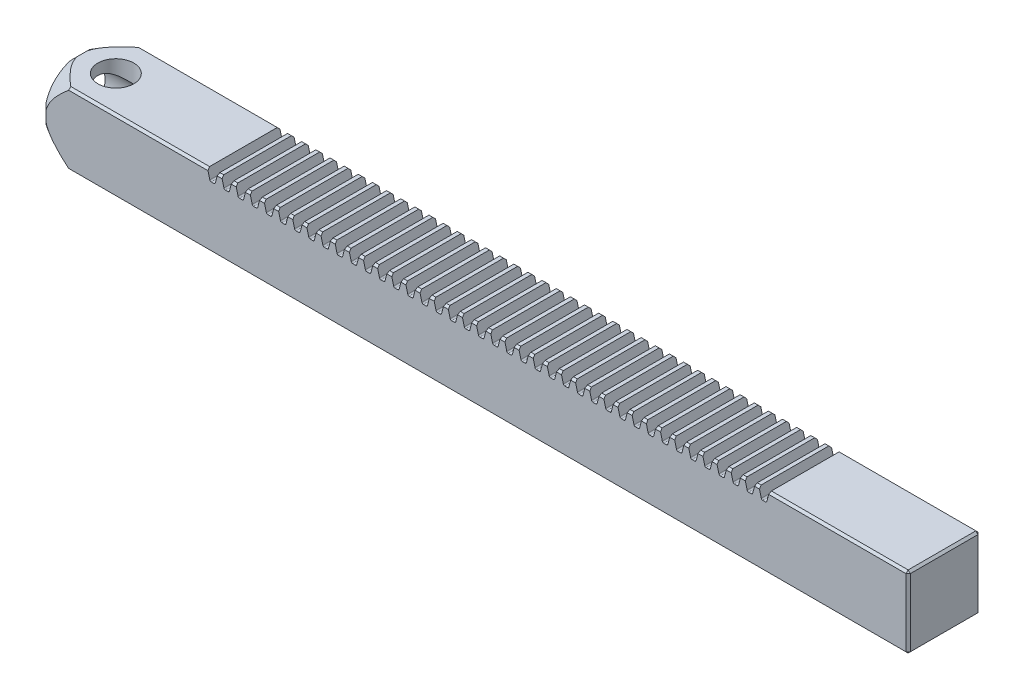
SolidWorks part; units mm, degrees
ref_plane "Front Plane" through (0, 0, 0) normal (0, 0, 1) x (1, 0, 0)
ref_plane "Top Plane" through (0, 0, 0) normal (0, 1, 0) x (1, 0, 0)
ref_plane "Right Plane" through (0, 0, 0) normal (1, 0, 0) x (0, 0, -1)
sketch "Sketch1" plane through (0, 0, 0) normal (1, 0, 0) x (0, 0, -1)
  line L1 (0.5, 0.5) -> (-0.5, 0.5)
  line L2 (0.5, 0.5) -> (0.5, -0.5)
  line L3 (0.5, -0.5) -> (-0.5, -0.5)
  line L4 (-0.5, 0.5) -> (-0.5, -0.5)
  line L5 (0.5, 0.5) -> (-0.5, -0.5) construction
  line L6 (0.5, -0.5) -> (-0.5, 0.5) construction
  point P0 (0, 0)
  dimension "D1" = 1
  dimension "D2" = 1
extrude "Boss-Extrude1" add sketch "Sketch1" along normal blind 12
chamfer "Chamfer1" distance 0.03 angle 45 12 edges at (12, 0, -0.5) (0, 0, -0.5) (12, -0.5, 0) (6, -0.5, -0.5) (0, -0.5, 0) (12, 0, 0.5) (6, -0.5, 0.5) (0, 0, 0.5) (6, 0.5, -0.5) (12, 0.5, 0) (6, 0.5, 0.5) (0, 0.5, 0)
sketch "Sketch2" plane through (0, 0, 0.5) normal (0, 0, 1) x (1, 0, 0)
  line L0 (10.0716, 0.5) -> (10.0384, 0.372)
  line L1 (0.03, 0.5) -> (11.97, 0.5) construction
  line L2 (10.0191, 0.357) -> (9.9809, 0.357)
  line L3 (9.9616, 0.372) -> (9.9284, 0.5)
  line L4 (10, 0.357) -> (10, 0.5547) construction
  line L5 (12, 0.47) -> (12, -0.47) construction
  line L6 (9.9284, 0.5) -> (10.0716, 0.5)
  arc A0 (10.0384, 0.372) -> (10.0191, 0.357) centre (10.0191, 0.377) cw
  arc A1 (9.9809, 0.357) -> (9.9616, 0.372) centre (9.9809, 0.377) cw
  point P8 (9.945, 0.436)
  point P9 (10.055, 0.436)
  dimension "D4" = 0.02
  dimension "D1" = 14.5
  dimension "D2" = 14.5
  dimension "D3" = 0.11
  dimension "D5" = 2
  dimension "D6" = 0.143
extrude "Cut-Extrude4" cut sketch "Sketch2" against normal blind 1 contours L0 A0 L2 A1 L3 L6
pattern_linear "LPattern1" count 40 spacing 0.1963 along (-1, 0, 0) of "Cut-Extrude4"
sketch "Sketch4" plane through (0, 0, 0) normal (-1, 0, 0) x (0, 0, 1)
  circle A0 centre (0, 0) radius 0.35
  dimension "D1" = 0.7
extrude "Cut-Extrude5" cut sketch "Sketch4" against normal blind 1
sketch "Sketch5" plane through (0, 0.5, 0) normal (0, 1, 0) x (1, 0, 0)
  line L0 (2.2786, -0.5) -> (0.03, -0.5) construction
  circle A0 centre (0.5, 0) radius 0.25
  dimension "D1" = 0.5
  dimension "D3" = 0.5
  dimension "D2" = 0.5
  dimension "D4" = 0.5
extrude "Cut-Extrude6" cut sketch "Sketch5" against normal up to next
sketch "Sketch6" plane through (0, 0, 0) normal (0, 0, 1) x (1, 0, 0)
  line L0 (0, 0.4874) -> (0, 0.6874)
  line L1 (0, 0.6874) -> (0.3464, 0.6874)
  line L2 (0.3464, 0.6874) -> (0, 0.4874)
  line L3 (0.03, 0.5) -> (2.2708, 0.5) construction
  line L4 (0, 0) -> (0.3566, 0) construction
  point P8 (0, 0)
  point P9 (0, 0)
  point P10 (0, 0)
  point P11 (0, 0)
  point P12 (0, 0)
  point P13 (0, 0.4881)
  point P14 (0, 0.4874)
  dimension "D1" = 0.2
  dimension "D2" = 30
revolve "Cut-Revolve1" cut sketch "Sketch6" angle 360 about L4
